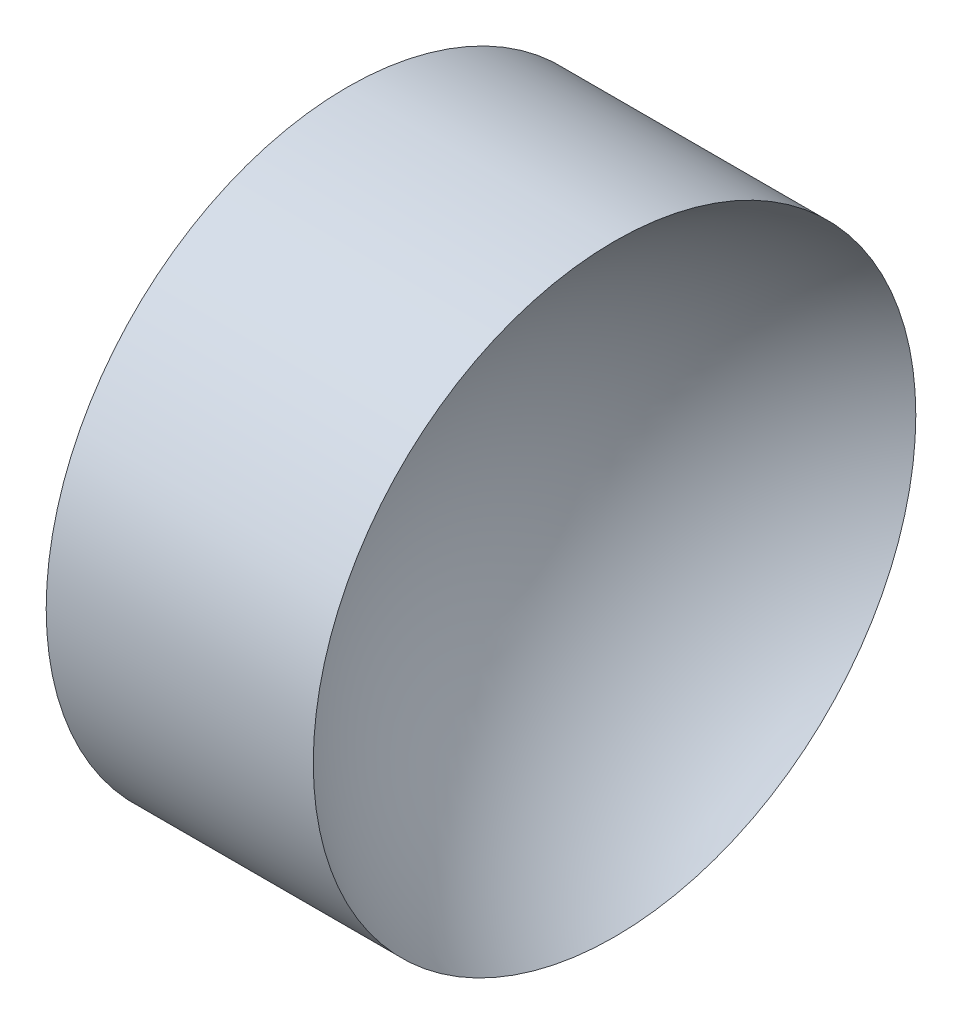
SolidWorks part; units mm, degrees
ref_plane "前视基准面" through (0, 0, 0) normal (0, 0, 1) x (1, 0, 0)
ref_plane "上视基准面" through (0, 0, 0) normal (0, 1, 0) x (1, 0, 0)
ref_plane "右视基准面" through (0, 0, 0) normal (1, 0, 0) x (0, 0, -1)
sketch "草图1" plane through (0, 0, 0) normal (0, 0, 1) x (1, 0, 0)
  line L0 (39.7365, 26.0623) -> (48.2578, 26.0623) construction
  line L1 (41.3658, 26.0623) -> (41.3658, 31.0623)
  line L2 (42.867, 26.0623) -> (41.3658, 26.0623)
  line L3 (41.3658, 31.0623) -> (45.7983, 31.0623)
  arc A0 (45.7983, 31.0623) -> (42.867, 26.0623) centre (48.597, 26.0623) ccw
revolve "旋转1" add sketch "草图1" angle 360 about L0
